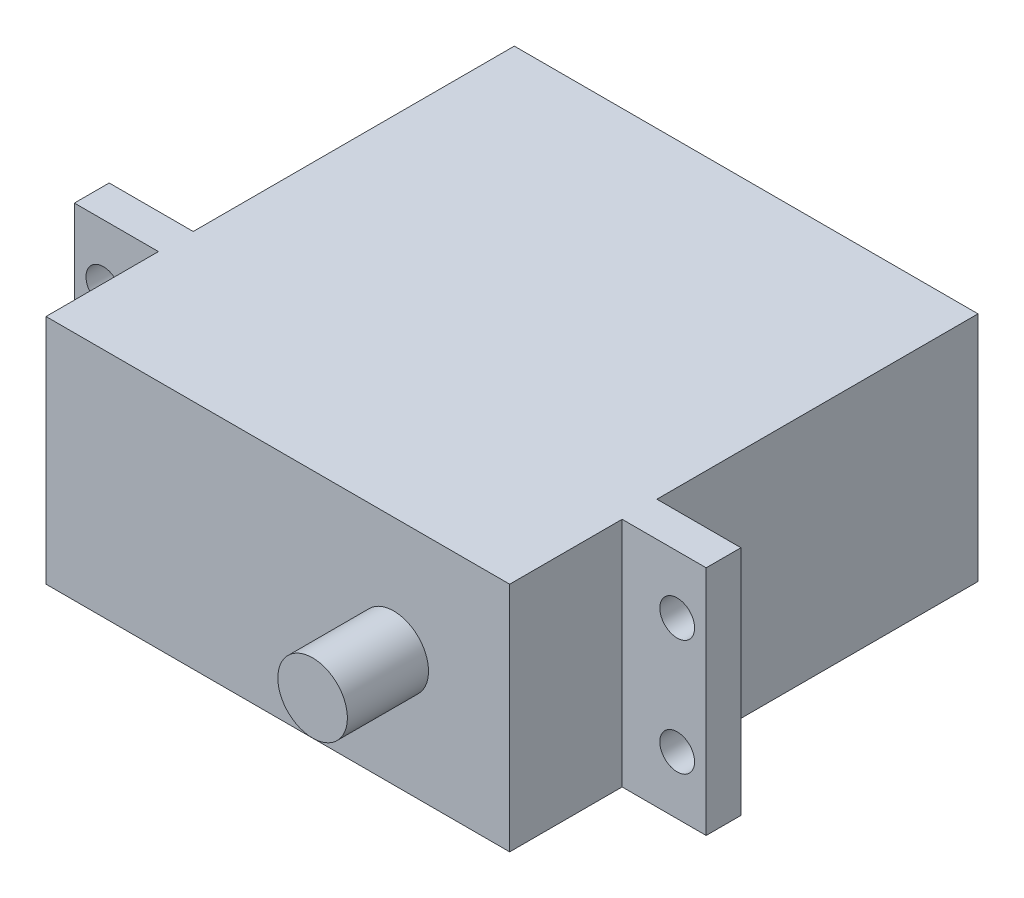
SolidWorks part; units mm, degrees
ref_plane "Front Plane" through (0, 0, 0) normal (0, 0, 1) x (1, 0, 0)
ref_plane "Top Plane" through (0, 0, 0) normal (0, 1, 0) x (1, 0, 0)
ref_plane "Right Plane" through (0, 0, 0) normal (1, 0, 0) x (0, 0, -1)
sketch "Sketch1" plane through (0, 0, 0) normal (0, 1, 0) x (1, 0, 0)
  line L1 (-27.6845, 15.2601) -> (12.3155, 15.2601)
  line L2 (-27.6845, 15.2601) -> (-27.6845, -25.1399)
  line L3 (-27.6845, -25.1399) -> (12.3155, -25.1399)
  line L4 (12.3155, 15.2601) -> (12.3155, -25.1399)
  dimension "D1" = 40
  dimension "D2" = 40.4
extrude "Boss-Extrude1" add sketch "Sketch1" along normal blind 20
sketch "Sketch3" plane through (12.3155, 0, 0) normal (1, 0, 0) x (0, 0, -1)
  line L0 (-25.1399, 20) -> (15.2601, 20) construction
  line L1 (-25.1399, 0) -> (15.2601, 0) construction
  line L2 (-15.4399, 20) -> (-12.4399, 20)
  line L3 (-15.4399, 20) -> (-15.4399, 0)
  line L4 (-15.4399, 0) -> (-12.4399, 0)
  line L5 (-12.4399, 20) -> (-12.4399, 0)
  line L7 (15.2601, 20) -> (15.2601, 0) construction
  dimension "D1" = 27.7
  dimension "D2" = 3
extrude "Boss-Extrude2" add sketch "Sketch3" along normal blind 7.25
sketch "Sketch4" plane through (0, 0, 0) normal (0, -1, 0) x (-1, 0, 0)
  line L0 (7.6845, -25.1399) -> (7.6845, 15.2601) construction
  line L1 (27.6845, -25.1399) -> (-12.3155, -25.1399) construction
  line L2 (-12.3155, 15.2601) -> (27.6845, 15.2601) construction
ref_plane "Plane1" through (-7.6845, 0, 0) normal (-1, 0, 0) x (0, 0, 1)
mirror "Mirror1" about plane through (-7.6845, 0, 0) normal (-1, 0, 0) of "Boss-Extrude2"
sketch "Sketch5" plane through (0, 0, 15.4399) normal (0, 0, 1) x (1, 0, 0)
  line L5 (-32.4345, 15) -> (17.0655, 15) construction
  line L6 (17.0655, 5) -> (-32.4345, 5) construction
  circle A0 centre (17.0655, 15) radius 1.5
  circle A1 centre (17.0655, 5) radius 1.5
  circle A2 centre (-32.4345, 15) radius 1.5
  circle A3 centre (-32.4345, 5) radius 1.5
  point P12 (0, 0)
  dimension "D2" = 3
  dimension "D3" = 3
  dimension "D4" = 3
  dimension "D5" = 3
  dimension "D1" = 10
  dimension "D6" = 49.5
  dimension "D10" = 10
  dimension "D11" = 49.5
extrude "Cut-Extrude1" cut sketch "Sketch5" against normal blind 7.25
sketch "Sketch6" plane through (0, 0, 25.1399) normal (0, 0, 1) x (1, 0, 0)
  line L0 (-27.6845, 20) -> (12.3155, 20) construction
  line L1 (-27.6845, 20) -> (-27.6845, 0) construction
  circle A0 centre (2.3155, 10) radius 3
  dimension "D1" = 10
  dimension "D2" = 30
extrude "Boss-Extrude3" add sketch "Sketch6" along normal blind 7
